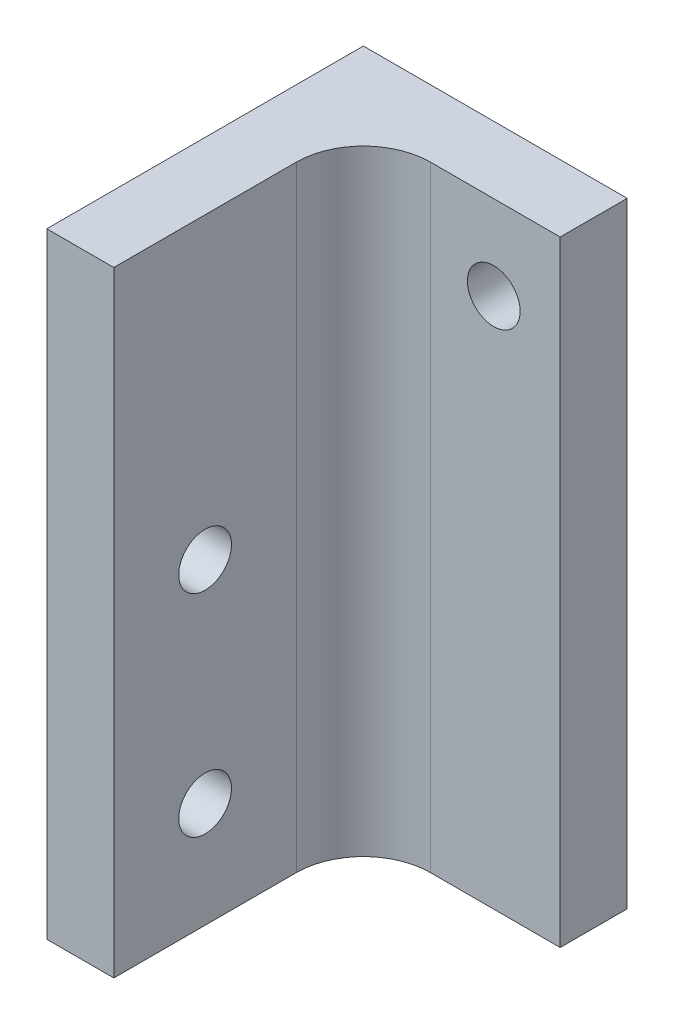
SolidWorks part; units mm, degrees
ref_plane "Front Plane" through (0, 0, 0) normal (0, 0, 1) x (1, 0, 0)
ref_plane "Top Plane" through (0, 0, 0) normal (0, 1, 0) x (1, 0, 0)
ref_plane "Right Plane" through (0, 0, 0) normal (1, 0, 0) x (0, 0, -1)
sketch "Sketch2" plane through (0, 0, 0) normal (0, 1, 0) x (1, 0, 0)
  line L0 (0, 0) -> (0, 30)
  line L1 (0, 30) -> (25, 30)
  line L2 (25, 30) -> (25, 23.65)
  line L3 (0, 0) -> (6.35, 0)
  line L4 (6.35, 0) -> (6.35, 17.3)
  line L5 (12.7, 23.65) -> (25, 23.65)
  arc A0 (6.35, 17.3) -> (12.7, 23.65) centre (12.7, 17.3) cw
  dimension "D4" = 6.35
  dimension "D1" = 6.35
  dimension "D2" = 6.35
  dimension "D3" = 30
  dimension "D5" = 25
extrude "Boss-Extrude1" add sketch "Sketch2" along normal blind 58.31
sketch "Sketch3" plane through (6.35, 0, 0) normal (1, 0, 0) x (0, 0, -1)
  line L1 (0, 10) -> (8.65, 10) construction
  line L3 (0, 58.31) -> (0, 0) construction
  line L4 (8.65, 10) -> (17.3, 10) construction
  line L5 (17.3, 58.31) -> (17.3, 0) construction
  line L6 (8.65, 10) -> (8.65, 30) construction
  line L7 (0, 0) -> (17.3, 0) construction
  circle A0 centre (8.65, 10) radius 2.5
  circle A1 centre (8.65, 30) radius 2.5
  dimension "D3" = 5
  dimension "D4" = 5
  dimension "D1" = 20
  dimension "D2" = 10
extrude "Cut-Extrude1" cut sketch "Sketch3" against normal through all
sketch "Sketch4" plane through (0, 0, -23.65) normal (0, 0, 1) x (1, 0, 0)
  line L0 (12.7, 0) -> (25, 0) construction
  circle A0 centre (18.7067, 50.31) radius 2.5
  dimension "D2" = 5
  dimension "D1" = 50.31
extrude "Cut-Extrude2" cut sketch "Sketch4" against normal through all
